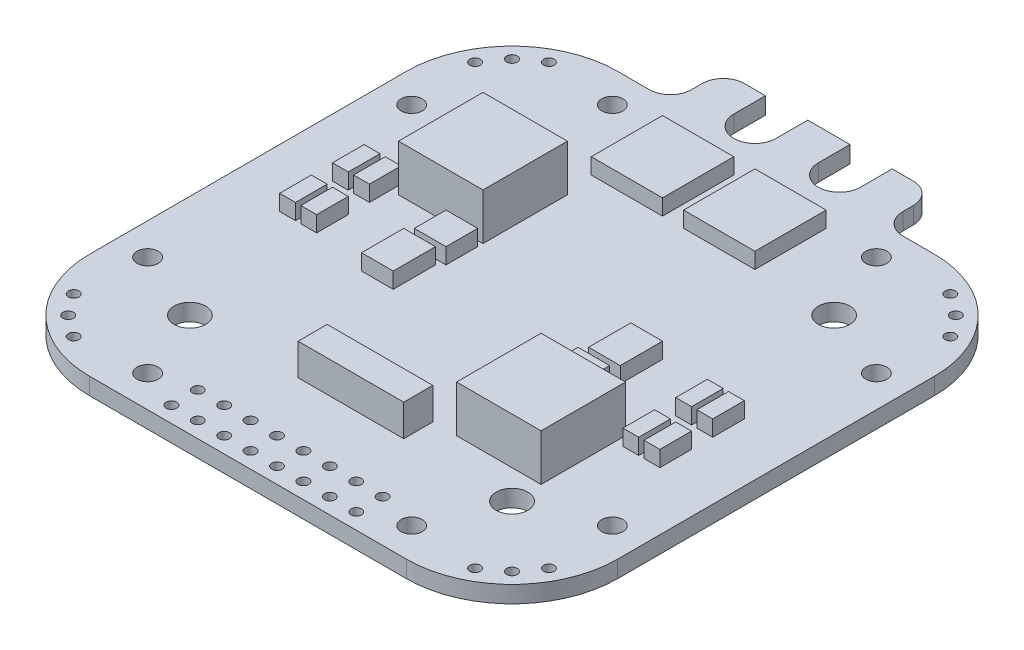
SolidWorks part; units mm, degrees
material "Commercially Pure CP-Ti UNS R50400 (SS)"
ref_plane "Front Plane" through (0, 0, 0) normal (0, 0, 1) x (1, 0, 0)
ref_plane "Top Plane" through (0, 0, 0) normal (0, 1, 0) x (1, 0, 0)
ref_plane "Right Plane" through (0, 0, 0) normal (1, 0, 0) x (0, 0, -1)
sketch "Sketch1" plane through (0, 0, 0) normal (0, 1, 0) x (1, 0, 0)
  line L1 (-25, -25) -> (25, -25) construction
  line L2 (-25, -25) -> (-25, 25) construction
  line L3 (-25, 25) -> (25, 25) construction
  line L4 (25, -25) -> (25, 25) construction
  line L5 (-25, -25) -> (25, 25) construction
  line L6 (-25, 25) -> (25, -25) construction
  line L7 (-10, 30) -> (10, 30) construction
  line L8 (-10, 30) -> (-10, 25) construction
  line L9 (-10, 25) -> (10, 25) construction
  line L10 (10, 30) -> (10, 25) construction
  line L11 (-10, 30) -> (10, 25) construction
  line L12 (-10, 25) -> (10, 30) construction
  line L13 (-10, 28) -> (-10, 27)
  line L14 (-12, 25) -> (-15, 25)
  line L15 (-25, 15) -> (-25, -15)
  line L16 (-15, -25) -> (15, -25)
  line L17 (0, 30) -> (0, -25) construction
  line L18 (10, 28) -> (10, 27)
  line L19 (12, 25) -> (15, 25)
  line L20 (25, 15) -> (25, -15)
  line L21 (-6, 27) -> (-6, 30)
  line L22 (-15.25, -15.25) -> (15.25, -15.25) construction
  line L23 (-15.25, -15.25) -> (-15.25, 15.25) construction
  line L24 (-15.25, 15.25) -> (15.25, 15.25) construction
  line L25 (15.25, -15.25) -> (15.25, 15.25) construction
  line L26 (-15.25, -15.25) -> (15.25, 15.25) construction
  line L27 (-15.25, 15.25) -> (15.25, -15.25) construction
  line L28 (-2, 27) -> (-2, 30)
  line L29 (2, 27) -> (2, 30)
  line L30 (6, 27) -> (6, 30)
  line L31 (-8, 30) -> (-6, 30)
  line L32 (-2, 30) -> (2, 30)
  line L33 (6, 30) -> (8, 30)
  line L34 (-12, 23.5) -> (-15, 23.5) construction
  line L35 (-22, -12.5) -> (22, -12.5) construction
  line L36 (-22, -12.5) -> (-22, 12.5) construction
  line L37 (-22, 12.5) -> (22, 12.5) construction
  line L38 (22, -12.5) -> (22, 12.5) construction
  line L39 (-22, -12.5) -> (22, 12.5) construction
  line L40 (-22, 12.5) -> (22, -12.5) construction
  line L41 (-12.5, -22) -> (12.5, -22) construction
  line L42 (-12.5, -22) -> (-12.5, 22) construction
  line L43 (-12.5, 22) -> (12.5, 22) construction
  line L44 (12.5, -22) -> (12.5, 22) construction
  line L45 (-12.5, -22) -> (12.5, 22) construction
  line L46 (-12.5, 22) -> (12.5, -22) construction
  line L47 (-8.5, 28) -> (-8.5, 27) construction
  line L48 (-8, 28.5) -> (-7.5, 28.5) construction
  line L49 (-7.5, 27) -> (-7.5, 28.5) construction
  line L50 (-0.5, 27) -> (-0.5, 28.5) construction
  line L51 (-0.5, 28.5) -> (0.5, 28.5) construction
  line L52 (0.5, 27) -> (0.5, 28.5) construction
  line L53 (7.5, 27) -> (7.5, 28.5) construction
  line L54 (7.5, 28.5) -> (8, 28.5) construction
  line L55 (8.5, 28) -> (8.5, 27) construction
  line L56 (12, 23.5) -> (15, 23.5) construction
  line L57 (23.5, 15) -> (23.5, -15) construction
  line L58 (-15, -23.5) -> (15, -23.5) construction
  line L59 (-23.5, 15) -> (-23.5, -15) construction
  arc A0 (-25, 15) -> (-15, 25) centre (-15, 15) cw
  arc A1 (-12, 25) -> (-10, 27) centre (-12, 27) ccw
  arc A2 (-8, 30) -> (-10, 28) centre (-8, 28) ccw
  arc A3 (-25, -15) -> (-15, -25) centre (-15, -15) ccw
  arc A4 (8, 30) -> (10, 28) centre (8, 28) cw
  arc A5 (12, 25) -> (10, 27) centre (12, 27) cw
  arc A6 (25, 15) -> (15, 25) centre (15, 15) ccw
  arc A7 (25, -15) -> (15, -25) centre (15, -15) cw
  circle A8 centre (15.25, -15.25) radius 1.5
  circle A9 centre (-15.25, -15.25) radius 1.5
  circle A10 centre (-15.25, 15.25) radius 1.5
  circle A11 centre (15.25, 15.25) radius 1.5
  arc A12 (2, 27) -> (6, 27) centre (4, 27) ccw
  arc A13 (-6, 27) -> (-2, 27) centre (-4, 27) ccw
  circle A14 centre (22, 12.5) radius 1
  circle A15 centre (22, -12.5) radius 1
  circle A16 centre (12.5, -22) radius 1
  circle A17 centre (-12.5, -22) radius 1
  circle A18 centre (-22, -12.5) radius 1
  circle A19 centre (-22, 12.5) radius 1
  circle A20 centre (-12.5, 22) radius 1
  circle A21 centre (12.5, 22) radius 1
  arc A22 (-23.5, 15) -> (-15, 23.5) centre (-15, 15) cw construction
  arc A23 (-12, 23.5) -> (-8.5, 27) centre (-12, 27) ccw construction
  arc A24 (-8, 28.5) -> (-8.5, 28) centre (-8, 28) ccw construction
  arc A25 (-7.5, 27) -> (-0.5, 27) centre (-4, 27) ccw construction
  arc A26 (0.5, 27) -> (7.5, 27) centre (4, 27) ccw construction
  arc A27 (8, 28.5) -> (8.5, 28) centre (8, 28) cw construction
  arc A28 (12, 23.5) -> (8.5, 27) centre (12, 27) cw construction
  arc A29 (23.5, 15) -> (15, 23.5) centre (15, 15) ccw construction
  arc A30 (23.5, -15) -> (15, -23.5) centre (15, -15) cw construction
  arc A31 (-23.5, -15) -> (-15, -23.5) centre (-15, -15) ccw construction
  circle A33 centre (-1.25, -23.5) radius 0.5
  circle A34 centre (1.25, -23.5) radius 0.5
  circle A35 centre (-3.75, -23.5) radius 0.5
  circle A36 centre (-6.25, -23.5) radius 0.5
  circle A37 centre (-8.75, -23.5) radius 0.5
  circle A38 centre (3.75, -23.5) radius 0.5
  circle A39 centre (6.25, -23.5) radius 0.5
  circle A40 centre (8.75, -23.5) radius 0.5
  circle A41 centre (-8.75, -21) radius 0.5
  circle A42 centre (-6.25, -21) radius 0.5
  circle A43 centre (-3.75, -21) radius 0.5
  circle A44 centre (-1.25, -21) radius 0.5
  circle A45 centre (1.25, -21) radius 0.5
  circle A46 centre (3.75, -21) radius 0.5
  circle A47 centre (6.25, -21) radius 0.5
  circle A48 centre (8.75, -21) radius 0.5
  circle A49 centre (-21.0104, -21.0104) radius 0.5
  circle A50 centre (-19.0019, -22.499) radius 0.5
  circle A51 centre (-22.499, -19.0019) radius 0.5
  circle A52 centre (-19.0019, 22.499) radius 0.5
  circle A53 centre (-21.0104, 21.0104) radius 0.5
  circle A54 centre (-22.499, 19.0019) radius 0.5
  circle A55 centre (22.499, 19.0019) radius 0.5
  circle A56 centre (21.0104, 21.0104) radius 0.5
  circle A57 centre (19.0019, 22.499) radius 0.5
  circle A58 centre (19.0019, -22.499) radius 0.5
  circle A59 centre (21.0104, -21.0104) radius 0.5
  circle A60 centre (22.499, -19.0019) radius 0.5
  point P0 (0, 0)
  point P6 (0, 27.5)
  point P37 (0, 0)
  point P52 (0, 0)
  point P61 (0, 0)
  dimension "D4" = 10
  dimension "D5" = 2
  dimension "D7" = 3
  dimension "D12" = 2
  dimension "D14" = 1
  dimension "D1" = 50
  dimension "D2" = 5
  dimension "D3" = 20
  dimension "D6" = 30.5
  dimension "D8" = 4
  dimension "D9" = 4
  dimension "D10" = 44
  dimension "D11" = 25
  dimension "D15" = 2.5
  dimension "D19" = 2.5
  dimension "D20" = 2.5
  dimension "D13" = 1.5
  dimension "D16" = 4
  dimension "D17" = 4
  dimension "D18" = 2
  dimension "D21" = 4
extrude "Boss-Extrude1" add sketch "Sketch1" along normal blind 1.6
sketch "Sketch2" plane through (0, 0, 0) normal (0, 1, 0) x (1, 0, 0)
  line L0 (-15.25, -15.25) -> (-15.25, 15.25) construction
  line L1 (-7.25, 4.5) -> (-15.25, 4.5)
  line L2 (-7.25, 4.5) -> (-7.25, 12.5)
  line L3 (-7.25, 12.5) -> (-15.25, 12.5)
  line L4 (-15.25, 4.5) -> (-15.25, 12.5)
  line L5 (-7.25, 4.5) -> (-15.25, 12.5) construction
  line L6 (-7.25, 12.5) -> (-15.25, 4.5) construction
  line L7 (15.25, -15.25) -> (15.25, 15.25) construction
  line L8 (7.25, -4.5) -> (15.25, -4.5)
  line L9 (7.25, -4.5) -> (7.25, -12.5)
  line L10 (7.25, -12.5) -> (15.25, -12.5)
  line L11 (15.25, -4.5) -> (15.25, -12.5)
  line L12 (7.25, -4.5) -> (15.25, -12.5) construction
  line L13 (7.25, -12.5) -> (15.25, -4.5) construction
  line L14 (-22, -12.5) -> (22, -12.5) construction
  line L15 (-22, 12.5) -> (22, 12.5) construction
  point P0 (-11.25, 8.5)
  point P7 (11.25, -8.5)
  dimension "D1" = 8
extrude "Boss-Extrude2" add sketch "Sketch2" along normal blind 4.4 from offset 1.6
sketch "Sketch3" plane through (0, 1.6, 0) normal (0, 1, 0) x (1, 0, 0)
  line L0 (0, 30) -> (0, -25) construction
  line L1 (-5, -12.5) -> (5, -12.5)
  line L2 (-5, -12.5) -> (-5, -15.25)
  line L3 (-5, -15.25) -> (5, -15.25)
  line L4 (5, -12.5) -> (5, -15.25)
  line L5 (-5, -12.5) -> (5, -15.25) construction
  line L6 (-5, -15.25) -> (5, -12.5) construction
  line L7 (-15.25, -15.25) -> (15.25, -15.25) construction
  line L8 (-22, -12.5) -> (22, -12.5) construction
  point P0 (0, -13.875)
  dimension "D1" = 10
  dimension "D2" = 2.75
extrude "Boss-Extrude3" add sketch "Sketch3" along normal blind 3
sketch "Sketch4" plane through (0, 1.6, 0) normal (0, 1, 0) x (1, 0, 0)
  line L0 (-12.5, 22) -> (12.5, 22) construction
  line L1 (-7.75, 15.25) -> (-1, 15.25)
  line L2 (-7.75, 15.25) -> (-7.75, 22)
  line L3 (-7.75, 22) -> (-1, 22)
  line L4 (-1, 15.25) -> (-1, 22)
  line L5 (-7.75, 15.25) -> (-1, 22) construction
  line L6 (-7.75, 22) -> (-1, 15.25) construction
  line L7 (15.25, -15.25) -> (15.25, 15.25) construction
  line L8 (1, 15.25) -> (7.75, 15.25)
  line L9 (1, 15.25) -> (1, 22)
  line L10 (1, 22) -> (7.75, 22)
  line L11 (7.75, 15.25) -> (7.75, 22)
  line L12 (1, 15.25) -> (7.75, 22) construction
  line L13 (1, 22) -> (7.75, 15.25) construction
  line L14 (-1, 22) -> (1, 15.25) construction
  line L15 (0, 30) -> (0, -25) construction
  line L16 (-15.25, 15.25) -> (15.25, 15.25) construction
  line L17 (7.25, -4.5) -> (7.25, -12.5) construction
  line L18 (7.25, -1) -> (10.25, -1)
  line L19 (7.25, -1) -> (7.25, -4)
  line L20 (7.25, -4) -> (10.25, -4)
  line L21 (10.25, -1) -> (10.25, -4)
  line L22 (7.25, -1) -> (10.25, -4) construction
  line L23 (7.25, -4) -> (10.25, -1) construction
  line L24 (15.25, -4.5) -> (7.25, -4.5) construction
  line L25 (10.75, 3.5) -> (7.75, 3.5)
  line L26 (10.75, 3.5) -> (10.75, -0.5)
  line L27 (10.75, -0.5) -> (7.75, -0.5)
  line L28 (7.75, 3.5) -> (7.75, -0.5)
  line L29 (10.75, 3.5) -> (7.75, -0.5) construction
  line L30 (10.75, -0.5) -> (7.75, 3.5) construction
  line L31 (17.5, -2.5) -> (16, -2.5)
  line L32 (17.5, -2.5) -> (17.5, -5.5)
  line L33 (17.5, -5.5) -> (16, -5.5)
  line L34 (16, -2.5) -> (16, -5.5)
  line L35 (17.5, -2.5) -> (16, -5.5) construction
  line L36 (17.5, -5.5) -> (16, -2.5) construction
  line L37 (-10.75, -3.5) -> (-10.75, 0.5)
  line L38 (17.5, 2.5) -> (16, 2.5)
  line L39 (17.5, 2.5) -> (17.5, -0.5)
  line L40 (17.5, -0.5) -> (16, -0.5)
  line L41 (16, 2.5) -> (16, -0.5)
  line L42 (17.5, 2.5) -> (16, -0.5) construction
  line L43 (17.5, -0.5) -> (16, 2.5) construction
  line L44 (19.5, 2.5) -> (18, 2.5)
  line L45 (19.5, 2.5) -> (19.5, -0.5)
  line L46 (19.5, -0.5) -> (18, -0.5)
  line L47 (18, 2.5) -> (18, -0.5)
  line L48 (19.5, 2.5) -> (18, -0.5) construction
  line L49 (19.5, -0.5) -> (18, 2.5) construction
  line L50 (19.5, -2.5) -> (18, -2.5)
  line L51 (19.5, -2.5) -> (19.5, -5.5)
  line L52 (19.5, -5.5) -> (18, -5.5)
  line L53 (18, -2.5) -> (18, -5.5)
  line L54 (19.5, -2.5) -> (18, -5.5) construction
  line L55 (19.5, -5.5) -> (18, -2.5) construction
  line L56 (18.75, -4) -> (16.75, -4) construction
  line L57 (18.75, -4) -> (18.75, 1) construction
  line L58 (18.75, 1) -> (16.75, 1) construction
  line L59 (16.75, -4) -> (16.75, 1) construction
  line L60 (18.75, -4) -> (16.75, 1) construction
  line L61 (18.75, 1) -> (16.75, -4) construction
  line L62 (-10.75, -3.5) -> (-7.75, -3.5)
  line L63 (-7.75, -3.5) -> (-7.75, 0.5)
  line L64 (-10.75, 0.5) -> (-7.75, 0.5)
  line L65 (-7.25, 1) -> (-7.25, 4)
  line L66 (-7.25, 1) -> (-10.25, 1)
  line L67 (-10.25, 1) -> (-10.25, 4)
  line L68 (-7.25, 4) -> (-10.25, 4)
  line L69 (-17.5, -2.5) -> (-17.5, 0.5)
  line L70 (-17.5, -2.5) -> (-16, -2.5)
  line L71 (-16, -2.5) -> (-16, 0.5)
  line L72 (-17.5, 0.5) -> (-16, 0.5)
  line L73 (-19.5, -2.5) -> (-19.5, 0.5)
  line L74 (-19.5, -2.5) -> (-18, -2.5)
  line L75 (-18, -2.5) -> (-18, 0.5)
  line L76 (-19.5, 0.5) -> (-18, 0.5)
  line L77 (-17.5, 2.5) -> (-17.5, 5.5)
  line L78 (-17.5, 2.5) -> (-16, 2.5)
  line L79 (-16, 2.5) -> (-16, 5.5)
  line L80 (-17.5, 5.5) -> (-16, 5.5)
  line L81 (-19.5, 2.5) -> (-19.5, 5.5)
  line L82 (-19.5, 2.5) -> (-18, 2.5)
  line L83 (-18, 2.5) -> (-18, 5.5)
  line L84 (-19.5, 5.5) -> (-18, 5.5)
  point P0 (-4.375, 18.625)
  point P7 (4.375, 18.625)
  point P12 (0, 18.625)
  point P17 (8.75, -2.5)
  point P24 (9.25, 1.5)
  point P31 (16.75, -4)
  point P38 (16.75, 1)
  point P43 (18.75, 1)
  point P48 (18.75, -4)
  point P57 (17.75, -1.5)
  dimension "D1" = 2
  dimension "D2" = 3
  dimension "D3" = 4
  dimension "D4" = 3
  dimension "D5" = 0.5
  dimension "D6" = 0.5
  dimension "D7" = 0.5
  dimension "D8" = 1.5
  dimension "D9" = 3
  dimension "D10" = 2
  dimension "D11" = 5
  dimension "D12" = 2.5
  dimension "D13" = 3
  dimension "D14" = 2
extrude "Boss-Extrude4" add sketch "Sketch4" along normal blind 1.5
